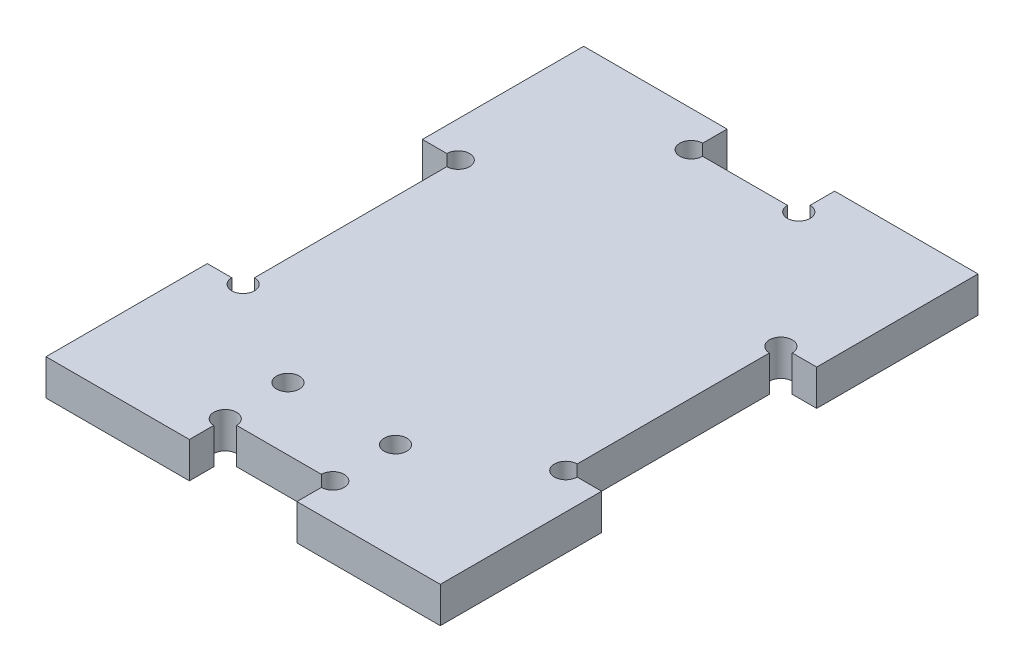
SolidWorks part; units mm, degrees
material "Acrylic (Medium-high impact)"
ref_plane "Front Plane" through (0, 0, 0) normal (0, 0, 1) x (1, 0, 0)
ref_plane "Top Plane" through (0, 0, 0) normal (0, 1, 0) x (1, 0, 0)
ref_plane "Right Plane" through (0, 0, 0) normal (1, 0, 0) x (0, 0, -1)
sketch "Sketch1" plane through (0, 0, 0) normal (0, 1, 0) x (1, 0, 0)
  line L1 (0, 0) -> (55, 0)
  line L2 (0, 0) -> (0, 75)
  line L3 (0, 75) -> (55, 75)
  line L4 (55, 0) -> (55, 75)
  dimension "D1" = 75
  dimension "D2" = 55
extrude "Boss-Extrude1" add sketch "Sketch1" along normal blind 5
sketch "Sketch3" plane through (0, 5, 0) normal (0, 1, 0) x (1, 0, 0)
  point P0 (15.5429, 20.9788)
sketch "Sketch5" plane through (0, 5, 0) normal (0, 1, 0) x (1, 0, 0)
  line L0 (0, 75) -> (0, 0) construction
  line L1 (0, 22.5) -> (5, 22.5)
  line L2 (0, 22.5) -> (0, 52.5)
  line L3 (0, 52.5) -> (5, 52.5)
  line L4 (5, 22.5) -> (5, 52.5)
  line L5 (55, 75) -> (0, 75) construction
  line L6 (35, 75) -> (20, 75)
  line L7 (35, 75) -> (35, 70)
  line L8 (35, 70) -> (20, 70)
  line L9 (20, 75) -> (20, 70)
  line L10 (55, 0) -> (55, 75) construction
  line L11 (55, 52.5) -> (50, 52.5)
  line L12 (55, 52.5) -> (55, 22.5)
  line L13 (55, 22.5) -> (50, 22.5)
  line L14 (50, 52.5) -> (50, 22.5)
  line L15 (0, 0) -> (55, 0) construction
  line L16 (20, 0) -> (35, 0)
  line L17 (20, 0) -> (20, 5)
  line L18 (20, 5) -> (35, 5)
  line L19 (35, 0) -> (35, 5)
  point P25 (0, 37.5)
  point P26 (27.5, 0)
  dimension "D1" = 5
  dimension "D2" = 30
  dimension "D3" = 15
extrude "Cut-Extrude3" cut sketch "Sketch5" against normal through all both and the other way through all
sketch "Sketch6" plane through (0, 5, 0) normal (0, 1, 0) x (1, 0, 0)
  line L0 (5, 22.5) -> (50, 22.5) construction
  line L1 (20, 5) -> (20, 22.5) construction
  line L2 (35, 5) -> (35, 22.5) construction
  circle A0 centre (5, 52.5) radius 1.5875
  circle A1 centre (5, 22.5) radius 1.5875
  circle A2 centre (20, 5) radius 1.5875
  circle A3 centre (35, 5) radius 1.5875
  circle A4 centre (50, 22.5) radius 1.5875
  circle A5 centre (50, 52.5) radius 1.5875
  circle A6 centre (35, 70) radius 1.5875
  circle A7 centre (20, 70) radius 1.5875
  circle A10 centre (20, 13.75) radius 1.5875
  circle A11 centre (35, 13.75) radius 1.5875
  dimension "D1" = 3.175
extrude "Cut-Extrude4" cut sketch "Sketch6" against normal through all
equation "\"cortador\"=3.175"
equation "\"D1@Sketch6\"=\"cortador\""
